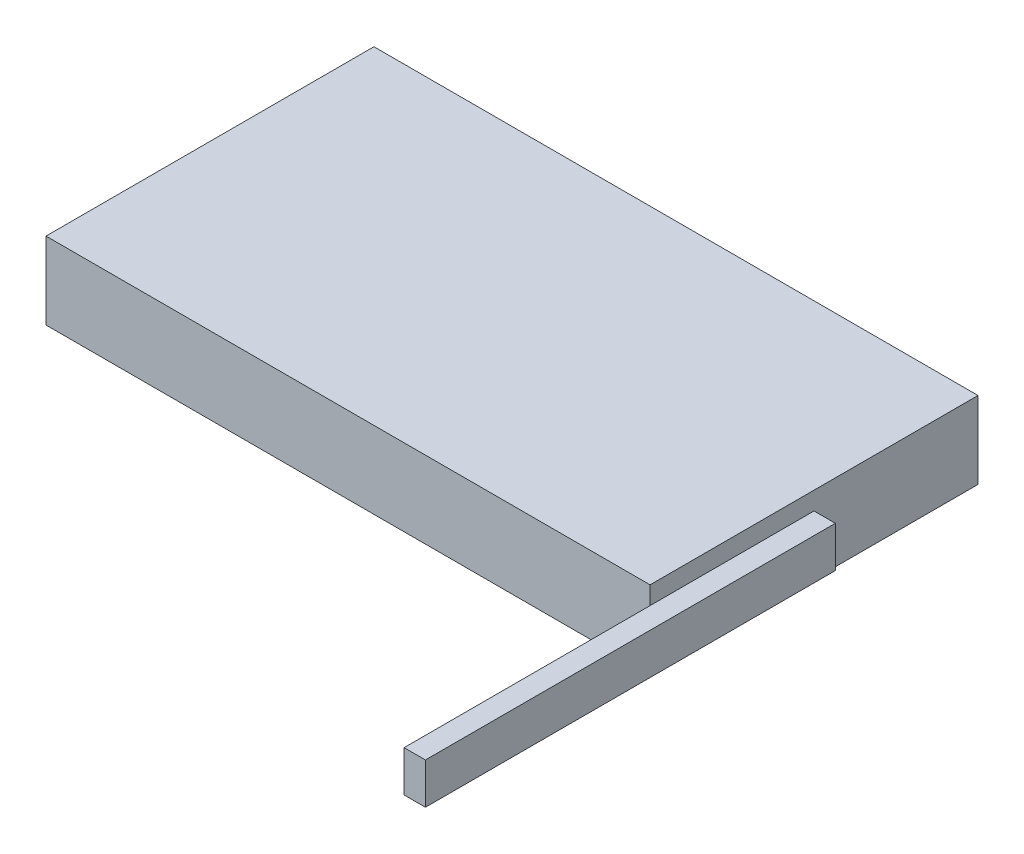
SolidWorks part; units mm, degrees
ref_plane "Front Plane" through (0, 0, 0) normal (0, 0, 1) x (1, 0, 0)
ref_plane "Top Plane" through (0, 0, 0) normal (0, 1, 0) x (1, 0, 0)
ref_plane "Right Plane" through (0, 0, 0) normal (1, 0, 0) x (0, 0, -1)
sketch "Sketch1" plane through (0, 0, 0) normal (0, 1, 0) x (1, 0, 0)
  line L1 (0, 0) -> (36.84, 0)
  line L2 (0, 0) -> (0, -20)
  line L3 (0, -20) -> (36.84, -20)
  line L4 (36.84, 0) -> (36.84, -20)
  dimension "D1" = 20
  dimension "D2" = 36.84
extrude "Boss-Extrude1" add sketch "Sketch1" along normal blind 4.7
sketch "Sketch2" plane through (0, 0, 20) normal (0, 0, 1) x (1, 0, 0)
  line L0 (36.84, 2.35) -> (38.14, 2.35) construction
  line L1 (36.84, 4.7) -> (36.84, 0) construction
  line L3 (36.84, 3.6) -> (38.14, 3.6)
  line L4 (36.84, 3.6) -> (36.84, 1.1)
  line L5 (36.84, 1.1) -> (38.14, 1.1)
  line L6 (38.14, 3.6) -> (38.14, 1.1)
  point P8 (0, 0)
  point P9 (37.3296, 2.35)
  dimension "D1" = 2.5
  dimension "D2" = 1.3
extrude "Boss-Extrude2" add sketch "Sketch2" along normal blind 15 and the other way blind 10
